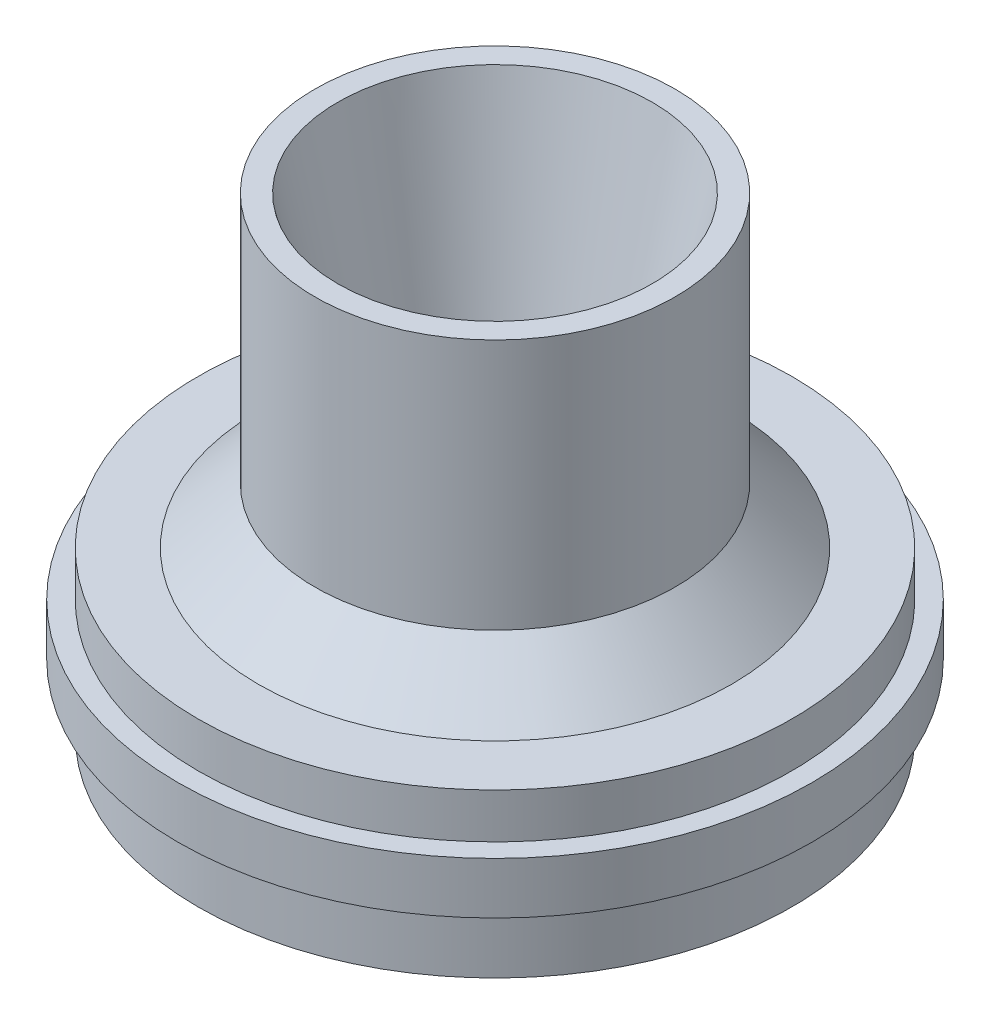
SolidWorks part; units mm, degrees
material "Graphite AR-12"
ref_plane "Front Plane" through (0, 0, 0) normal (0, 0, 1) x (1, 0, 0)
ref_plane "Top Plane" through (0, 0, 0) normal (0, 1, 0) x (1, 0, 0)
ref_plane "Right Plane" through (0, 0, 0) normal (1, 0, 0) x (0, 0, -1)
sketch "Sketch1" plane through (0, 0, 0) normal (0, 0, 1) x (1, 0, 0)
  line L0 (0, 0) -> (0, 25.4) construction
  line L1 (0, 25.4) -> (-22.7457, 25.4) construction
  line L2 (-22.7457, 25.4) -> (-13.589, -17.3482)
  line L3 (-13.589, -17.3482) -> (-13.589, -29.2862)
  line L4 (-40.513, -42.5704) -> (-42.926, -42.5704)
  line L5 (-42.926, -42.5704) -> (-42.926, -32.9946)
  line L6 (-42.926, -32.9946) -> (-45.847, -32.9946)
  line L7 (-45.847, -32.9946) -> (-45.847, -25.527)
  line L8 (-45.847, -25.527) -> (-42.926, -25.527)
  line L9 (-42.926, -25.527) -> (-42.926, -19.0246)
  line L10 (-42.926, -19.0246) -> (-34.2265, -19.0246)
  line L11 (-26.0477, -10.9474) -> (-34.2265, -19.0246)
  line L12 (-26.0477, -10.9474) -> (-26.0477, 25.4)
  line L13 (-26.0477, 25.4) -> (-22.7457, 25.4)
  line L14 (-13.589, -29.2862) -> (-40.513, -42.5704)
  dimension "D2" = 11.938
  dimension "D3" = 67.9704
  dimension "D4" = 13.589
  dimension "D5" = 9.5758
  dimension "D6" = 7.4676
  dimension "D7" = 34.2265
  dimension "D8" = 23.5458
  dimension "D9" = 26.0477
  dimension "D10" = 2.413
  dimension "D11" = 36.3474
  dimension "D12" = 25.4
  dimension "D13" = 3.302
  dimension "D14" = 42.926
  dimension "D15" = 45.847
  dimension "D16" = 42.7482
revolve "Revolve1" add sketch "Sketch1" angle 360 about L0
sketch "Sketch2" plane through (0, 25.4, 0) normal (0, 1, 0) x (1, 0, 0)
  point P0 (0, 0)
